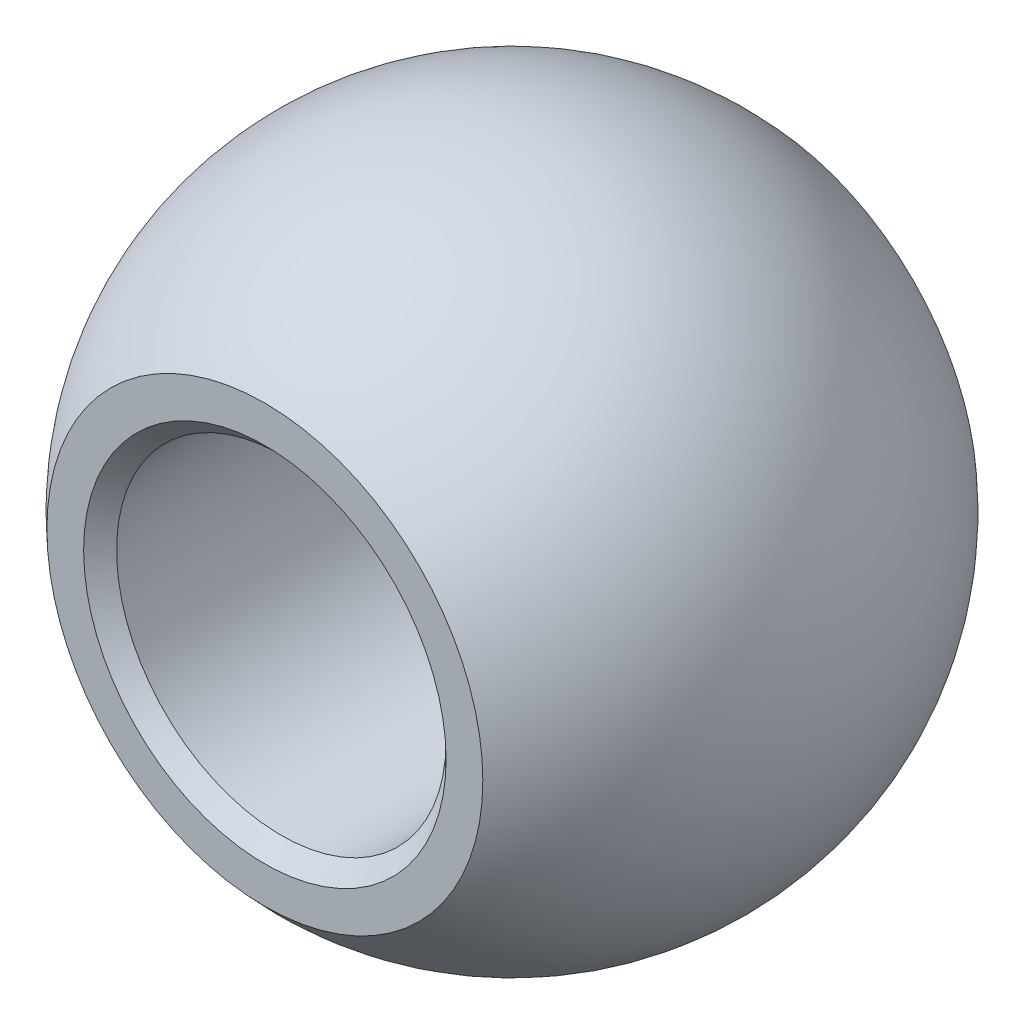
SolidWorks part; units mm, degrees
ref_plane "Front" through (0, 0, 0) normal (0, 0, 1) x (1, 0, 0)
ref_plane "Top" through (0, 0, 0) normal (0, 1, 0) x (1, 0, 0)
ref_plane "Right" through (0, 0, 0) normal (1, 0, 0) x (0, 0, -1)
sketch "Sketch1" plane through (0, 0, 0) normal (0, 0, 1) x (1, 0, 0)
  line L0 (0, 0) -> (0, -25.4)
  line L1 (0, -25.4) -> (3.175, -25.4)
  line L2 (3.175, -25.4) -> (3.175, 0)
  line L3 (3.175, 0) -> (0, 0)
  line L5 (0, 23.8125) -> (0, 0) construction
  line L6 (0, 23.8125) -> (9.525, 23.8125) construction
  line L7 (9.525, 23.8125) -> (9.525, 14.2875) construction
  line L8 (-3.175, -25.4) -> (-3.175, 0) construction
  line L9 (3.2732, -25.3433) -> (3.2732, -26.2501)
  line L10 (3.2732, -26.2501) -> (2.4879, -25.7967)
  line L11 (2.586, -25.8534) -> (2.586, -25.74)
  line L12 (2.4879, -25.7967) -> (3.2732, -25.3433)
  line L13 (3.2241, -25.3717) -> (3.2241, -26.2218)
  line L14 (3.2732, -25.7967) -> (3.175, -25.7967)
  line L15 (3.175, -25.4) -> (3.175, -26.1934)
  line L16 (2.4879, -25.7967) -> (2.586, -25.7967)
  arc A0 (6.3827, 7.2174) -> (0, 23.8125) centre (0, 14.2875) ccw construction
  circle A1 centre (0, 14.2875) radius 3.175 construction
  circle A2 centre (0, 14.2875) radius 6.35 construction
  circle A3 centre (0, 14.2875) radius 6.4135 construction
  arc A4 (3.175, 0) -> (6.3827, 7.2174) centre (12.8984, 0) cw construction
  point P24 (0, 20.6375)
  point P26 (3.175, -25.7967)
  point P28 (3.2241, -25.7967)
  dimension "A" = 6.35
  dimension "Ball Dia" = 12.7
  dimension "B" = 19.05
  dimension "D1" = 12.827
  dimension "D" = 39.6875
  dimension "E" = 25.4
  dimension "Thread Dia" = 6.35
  dimension "D2" = 60
  dimension "Pitch" = 0.9068
  dimension "D4" = 0.1133
sketch "Sketch2" plane through (0, 0, 0) normal (1, 0, 0) x (0, 0, -1)
  line L0 (3.175, 14.2875) -> (-3.175, 14.2875)
  line L1 (3.175, 15.0498) -> (0, 14.2875) construction
  line L2 (3.175, 13.5252) -> (0, 14.2875) construction
  line L6 (4.7625, 14.2875) -> (-4.7625, 14.2875)
  line L7 (0, 11.1125) -> (0, 17.4625)
  line L8 (0, 23.8125) -> (0, 0) construction
  line L9 (0, 17.4625) -> (0, 11.1125) construction
  circle A0 centre (0, 14.2875) radius 6.35
  circle A1 centre (0, 14.2875) radius 9.525
  point P4 (0, 14.2875)
  point P7 (0, 20.6375)
  point P9 (0, 7.9375)
  point P14 (0, 14.2875)
  point P18 (0, 14.2875)
  point P23 (9.525, 14.2875)
  point P25 (-9.525, 14.2875)
  dimension "OAWidth" = 6.35
  dimension "Swivel" = 27
  dimension "BallWidth" = 9.525
sketch "Sketch15" plane through (0, 0, 0) normal (0, 0, 1) x (1, 0, 0)
  line L0 (0, 23.8125) -> (0, 0) construction
  line L1 (9.525, 23.8125) -> (-9.525, 23.8125)
  line L2 (9.525, 23.8125) -> (9.525, 0)
  line L3 (9.525, 0) -> (-9.525, 0)
  line L4 (-9.525, 23.8125) -> (-9.525, 0)
  line L5 (3.175, 0) -> (0, 0) construction
  point P5 (0, 23.8125)
sketch "Sketch17" plane through (0, 0, 0) normal (0, 0, 1) x (1, 0, 0)
  circle A2 centre (0, 14.2875) radius 6.4135 construction
  circle A3 centre (0, 14.2875) radius 6.4135
sketch "Sketch7" plane through (0, 0, 0) normal (0, 0, 1) x (1, 0, 0)
  line L0 (0, 20.6375) -> (0, 7.9375)
  line L1 (0, 23.8125) -> (0, 0) construction
  line L2 (0, 0) -> (0, 7.9375) construction
  arc A0 (0, 7.9375) -> (0, 20.6375) centre (0, 14.2875) ccw
  circle A1 centre (0, 14.2875) radius 6.35 construction
revolve "Revolve3" add sketch "Sketch7" angle 360 about L2
sketch "Sketch10" plane through (0, 0, 0) normal (0, 0, 1) x (1, 0, 0)
  circle A0 centre (0, 14.2875) radius 3.175 construction
  circle A1 centre (0, 14.2875) radius 3.175
extrude "Cut-Extrude4" cut sketch "Sketch10" against normal through all and the other way through all
sketch "Sketch22" plane through (0, 0, 0) normal (0, 0, 1) x (1, 0, 0)
  line L0 (-9.525, 23.8125) -> (-9.525, 0) construction
  line L1 (9.525, 0) -> (-9.525, 0) construction
  line L2 (9.525, 23.8125) -> (9.525, 0) construction
  line L3 (9.525, 23.8125) -> (-9.525, 23.8125) construction
  line L4 (-9.525, 23.8125) -> (-9.525, 0)
  line L5 (9.525, 0) -> (-9.525, 0)
  line L6 (9.525, 23.8125) -> (9.525, 0)
  line L7 (9.525, 23.8125) -> (-9.525, 23.8125)
extrude "Cut-Extrude7" cut sketch "Sketch22" against normal through all from vertex at -4.7625 starting at point (0, 14.2875, -4.7625)
sketch "Sketch23" plane through (0, 0, 0) normal (0, 0, 1) x (1, 0, 0)
  line L0 (-9.525, 23.8125) -> (-9.525, 0) construction
  line L1 (9.525, 0) -> (-9.525, 0) construction
  line L2 (9.525, 23.8125) -> (9.525, 0) construction
  line L3 (9.525, 23.8125) -> (-9.525, 23.8125) construction
  line L4 (-9.525, 23.8125) -> (-9.525, 0)
  line L5 (9.525, 0) -> (-9.525, 0)
  line L6 (9.525, 23.8125) -> (9.525, 0)
  line L7 (9.525, 23.8125) -> (-9.525, 23.8125)
extrude "Cut-Extrude8" cut sketch "Sketch23" along normal through all from vertex at 4.7625 starting at point (0, 14.2875, 4.7625)
chamfer "Chamfer2" distance 0.3175 angle 45 2 edges at (3.175, 14.2875, 4.7625) (3.175, 14.2875, -4.7625)
ref_point "Swivel Center"
equation "\"D1@Sketch1\"=\"Ball Dia@Sketch1\"*1.01"
equation "\"D1\"= \"A@Sketch1\" / 20"
equation "\"D3\"= \"E@Sketch1\" + .2"
equation "\"D4@Sketch1\"=\"Pitch@Sketch1\"/8"
equation "\"D1@Chamfer2\"=\"A@Sketch1\"/20"
